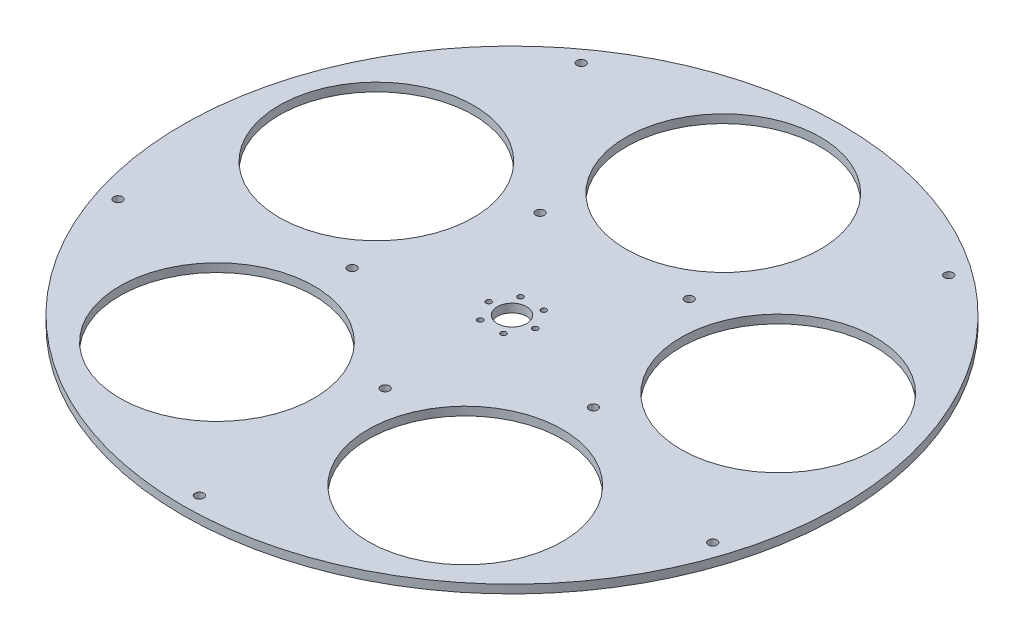
SolidWorks part; units mm, degrees
material "PC High Viscosity"
ref_plane "Front Plane" through (0, 0, 0) normal (0, 0, 1) x (1, 0, 0)
ref_plane "Top Plane" through (0, 0, 0) normal (0, 1, 0) x (1, 0, 0)
ref_plane "Right Plane" through (0, 0, 0) normal (1, 0, 0) x (0, 0, -1)
sketch "Sketch1" plane through (0, 0, 0) normal (0, 1, 0) x (1, 0, 0)
  circle A0 centre (0, 0) radius 247.65
  circle A1 centre (0, 158.75) radius 73.025
  circle A2 centre (150.9802, 49.0564) radius 73.025
  circle A3 centre (93.3109, -128.4314) radius 73.025
  circle A4 centre (-93.3109, -128.4314) radius 73.025
  circle A5 centre (-150.9802, 49.0564) radius 73.025
  point P6 (0, 247.65)
  point P15 (0, 0)
  dimension "D1" = 88.9
  dimension "D2" = 146.05
  dimension "D3" = 158.75
  dimension "D4" = 5
extrude "Boss-Extrude1" add sketch "Sketch1" along normal blind 6.35
sketch "Sketch3" plane through (-5.1845, 6.35, -2.4486) normal (0, 1, 0) x (1, 0, 0)
  circle A0 centre (5.1845, -2.4486) radius 11
  circle A1 centre (5.1845, -2.4486) radius 247.65 construction
  dimension "D1" = 22
extrude "Cut-Extrude1" cut sketch "Sketch3" against normal through all
hole_wizard "#10-32 Tapped Hole1" positions "Sketch5" profile "Sketch7" tap size "#10-32" standard "ANSI Inch" end condition through all
sketch "Sketch5" plane through (-5.1845, 6.35, -2.4486) normal (0, 1, 0) x (1, 0, 0)
  line L0 (5.1845, -2.4486) -> (-3.5467, 12.6744) construction
  line L2 (5.1845, -2.4486) -> (5.1845, 15.0139) construction
  circle A0 centre (5.1845, -2.4486) radius 17.4625
  point P0 (-3.5467, 12.6744)
  point P22 (13.9158, 12.6744)
  point P23 (22.647, -2.4486)
  point P24 (13.9158, -17.5715)
  point P25 (-3.5467, -17.5715)
  point P26 (-12.278, -2.4486)
  dimension "D1" = 34.925
  dimension "D2" = 30
  dimension "D3" = 6
sketch "Sketch7" plane through (-8.7313, 6.35, -15.123) normal (1, 0, 0) x (0, 0, 1)
  line L0 (0, 0) -> (0, 6.35)
  line L1 (0, 6.35) -> (2.0193, 6.35)
  line L2 (2.0193, 6.35) -> (2.0193, 0)
  line L5 (2.0193, 0) -> (0, 0)
  line L11 (0, -6.35) -> (0, 107.95) construction
  dimension "Thru Tap Drill Dia." = 4.0386
  dimension "Thru Tap Drill Depth" = 6.35
cosmetic thread "Hole Thread1" parameters "D2"=4.826
cosmetic thread "Hole Thread2" parameters "D2"=4.826
cosmetic thread "Hole Thread3" parameters "D2"=4.826
cosmetic thread "Hole Thread4" parameters "D2"=4.826
cosmetic thread "Hole Thread5" parameters "D2"=4.826
cosmetic thread "Hole Thread6" parameters "D2"=4.826
sketch "Sketch8" plane through (0, 6.35, 0) normal (0, 1, 0) x (1, 0, 0)
  circle A0 centre (0, -234.95) radius 3.2512
  circle A1 centre (-223.4507, -72.6035) radius 3.2512
  circle A2 centre (-138.1001, 190.0785) radius 3.2512
  circle A3 centre (138.1001, 190.0785) radius 3.2512
  circle A4 centre (223.4507, -72.6035) radius 3.2512
  circle A5 centre (0, 0) radius 247.65 construction
  point P14 (0, 0)
  dimension "D2" = 6.5024
  dimension "D1" = 234.95
  dimension "D3" = 5
extrude "Cut-Extrude2" cut sketch "Sketch8" against normal through all
sketch "Sketch9" plane through (0, 6.35, 0) normal (0, 1, 0) x (1, 0, 0)
  line L0 (0, -95.3389) -> (0, 0)
  circle A0 centre (0, 0) radius 95.3389 construction
  circle A1 centre (0, -95.3389) radius 3.2639
  dimension "D1" = 190.6778
  dimension "D2" = 6.5278
extrude "Cut-Extrude3" cut sketch "Sketch9" against normal through all contours A1
pattern_circular "CirPattern1" count 5 over 360 about axis through (0, 0, 0) along (0, 1, 0) of "Cut-Extrude3"
